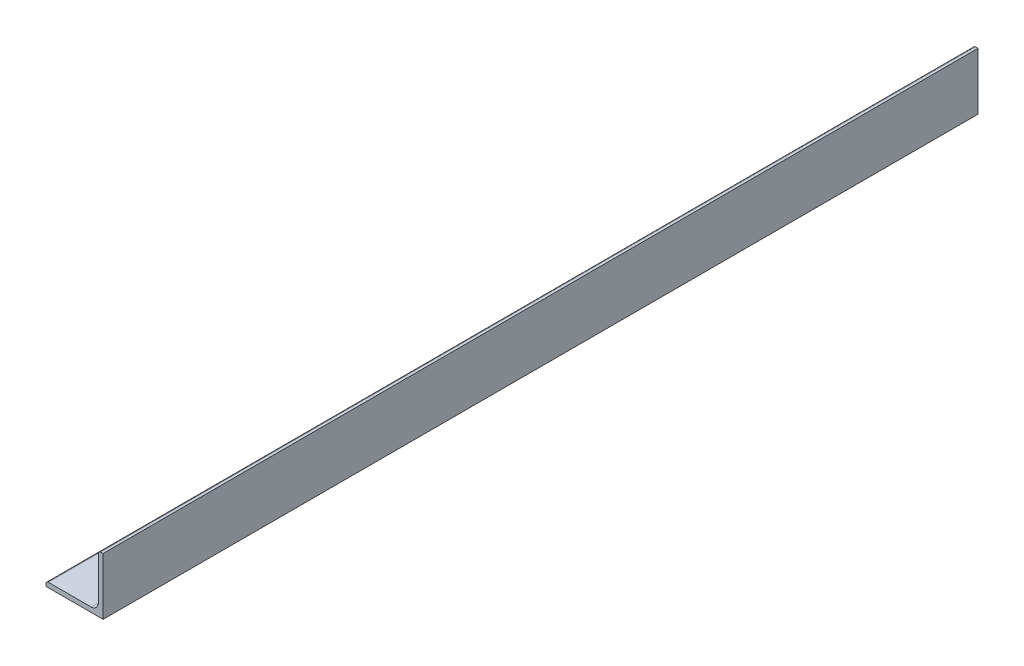
SolidWorks part; units mm, degrees
ref_plane "Front Plane" through (0, 0, 0) normal (0, 0, 1) x (1, 0, 0)
ref_plane "Top Plane" through (0, 0, 0) normal (0, 1, 0) x (1, 0, 0)
ref_plane "Right Plane" through (0, 0, 0) normal (1, 0, 0) x (0, 0, -1)
sketch "Sketch0" plane through (0, 0, 0) normal (0, 0, 1) x (1, 0, 0)
  line L0 (-19.05, -19.05) -> (19.05, -19.05)
  line L1 (19.05, -19.05) -> (19.05, 19.05)
  line L2 (19.05, 0) -> (0, 0) construction
  line L3 (0, 0) -> (0, -19.05) construction
  line L4 (15.875, -11.0998) -> (15.875, 19.05) construction
  line L5 (11.0998, -15.875) -> (-19.05, -15.875) construction
  arc A0 (15.875, -11.0998) -> (11.0998, -15.875) centre (11.0998, -11.0998) cw
  point P3 (14.4764, -14.4764)
  dimension "Inside Corner Radius" = 4.7752
  dimension "Outside Height" = 38.1
  dimension "Inside Height" = 34.925
  dimension "Inside Width" = 34.925
  dimension "Wall Thickness" = 3.175
  dimension "D1" = 3.175
  dimension "Outside Width" = 38.1
sketch "Sketch1" plane through (0, 0, 0) normal (1, 0, 0) x (0, 0, -1)
  line L0 (609.6, 0) -> (-609.6, 0)
  point P4 (0, 0)
  dimension "Length" = 1219.2
sketch "Sketch2" plane through (0, 0, 0) normal (0, 0, 1) x (1, 0, 0)
  line L0 (-19.05, -19.05) -> (19.05, -19.05)
  line L1 (19.05, -19.05) -> (19.05, 19.05)
  line L2 (19.05, 19.05) -> (15.875, 19.05) construction
  line L3 (15.875, 17.4625) -> (15.875, -11.0998)
  line L4 (11.0998, -15.875) -> (-17.4625, -15.875)
  line L5 (-19.05, -19.05) -> (-19.05, -15.875) construction
  line L6 (17.4625, 19.05) -> (19.05, 19.05)
  line L7 (-19.05, -17.4625) -> (-19.05, -19.05)
  line L8 (19.05, 0) -> (0, 0) construction
  line L9 (0, 0) -> (0, -19.05) construction
  arc A0 (15.875, 17.4625) -> (17.4625, 19.05) centre (17.4625, 17.4625) cw
  arc A1 (-19.05, -17.4625) -> (-17.4625, -15.875) centre (-17.4625, -17.4625) cw
  arc A2 (15.875, -11.0998) -> (11.0998, -15.875) centre (11.0998, -11.0998) cw
  dimension "Inside Radius" = 4.7752
  dimension "Height" = 38.1
  dimension "Width" = 38.1
  dimension "Thickness" = 3.175
extrude "Boss-Extrude1" add sketch "Sketch2" along normal mid plane 1219.2
sketch "Break Locations" plane through (0, 0, 0) normal (1, 0, 0) x (0, 0, -1)
  line L0 (-570.738, 0) -> (570.738, 0)
  line L1 (-609.6, -19.05) -> (-609.6, 19.05) construction
  line L2 (609.6, -19.05) -> (609.6, 19.05) construction
  point P0 (-577.215, 0)
  point P1 (577.215, 0)
  point P10 (0, 0)
  point P11 (570.738, 0)
  point P13 (-570.738, 0)
  dimension "D1" = 32.385
  dimension "D2" = 32.385
  dimension "D3" = 38.862
sketch "Sketch3" plane through (19.05, 0, 0) normal (1, 0, 0) x (0, 0, -1)
  line L5 (-609.6, -19.05) -> (609.6, -19.05) construction
  line L6 (609.6, 19.05) -> (-25.6, 19.05)
  line L7 (609.6, 19.05) -> (609.6, -19.05)
  line L8 (609.6, -19.05) -> (-25.6, -19.05)
  line L9 (-25.6, 19.05) -> (-25.6, -19.05)
  line L10 (-609.6, -19.05) -> (-609.6, 19.05) construction
  dimension "D1" = 584
extrude "Cut-Extrude1" cut sketch "Sketch3" against normal blind 60 contours L7 L6 L9 L8
equation "\"D1@Break Locations\" = .85 * \"Height@Sketch2\""
equation "\"D2@Break Locations\"=\"D1@Break Locations\""
equation "\"Thickness@Sketch2\" = \"Wall Thickness@Sketch0\""
equation "\"Height@Sketch2\" = \"Outside Height@Sketch0\""
equation "\"Width@Sketch2\" = \"Outside Width@Sketch0\""
equation "\"Inside Radius@Sketch2\" = \"Inside Corner Radius@Sketch0\""
equation "\"Length@Boss-Extrude1\" = \"Length@Sketch1\""
equation "\"D3@Break Locations\"=\"D2@Break Locations\"*1.2"
equation "\"D1@Sketch0\"=\"Wall Thickness@Sketch0\""
